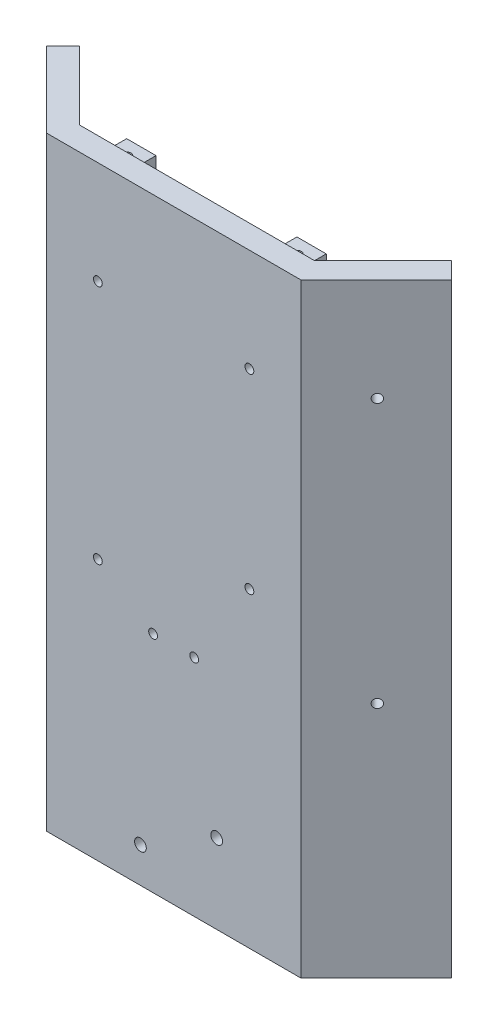
SolidWorks part; units mm, degrees
ref_plane "Front" through (0, 0, 0) normal (0, 0, 1) x (1, 0, 0)
ref_plane "Top" through (0, 0, 0) normal (0, 1, 0) x (1, 0, 0)
ref_plane "Right" through (0, 0, 0) normal (1, 0, 0) x (0, 0, -1)
sketch "Sketch1" plane through (0, 0, 0) normal (0, 1, 0) x (1, 0, 0)
  line L0 (-40, 0) -> (40, 0)
  line L1 (40, 0) -> (63.3345, 23.3345)
  line L2 (-40, 0) -> (-63.3345, 23.3345)
  line L3 (-43.3137, -8) -> (-68.9914, 17.6777)
  line L4 (-43.3137, -8) -> (43.3137, -8)
  line L5 (43.3137, -8) -> (68.9914, 17.6777)
  line L6 (-68.9914, 17.6777) -> (-63.3345, 23.3345)
  line L7 (68.9914, 17.6777) -> (63.3345, 23.3345)
  dimension "D1" = 80
  dimension "D2" = 33
  dimension "D3" = 33
  dimension "D4" = 135
  dimension "D5" = 135
  dimension "D6" = 8
extrude "Boss-Extrude1" add sketch "Sketch1" along normal blind 206
sketch "Sketch2" plane through (0, 0, 0) normal (0, 0, -1) x (-1, 0, 0)
  line L0 (-40, 206) -> (40, 206) construction
  line L1 (-34, 200) -> (-24, 200)
  line L2 (-34, 200) -> (-34, 194)
  line L3 (-34, 194) -> (-24, 194)
  line L4 (-24, 200) -> (-24, 194)
  line L5 (-34, 200) -> (-24, 194) construction
  line L6 (-34, 194) -> (-24, 200) construction
  line L7 (-40, 206) -> (-40, 0) construction
  line L8 (40, 206) -> (40, 0) construction
  line L9 (24, 200) -> (34, 200)
  line L10 (24, 200) -> (24, 194)
  line L11 (24, 194) -> (34, 194)
  line L12 (34, 200) -> (34, 194)
  line L13 (24, 200) -> (34, 194) construction
  line L14 (24, 194) -> (34, 200) construction
  point P0 (-29, 197)
  point P9 (29, 197)
  dimension "D1" = 6
  dimension "D2" = 10
  dimension "D3" = 6
  dimension "D4" = 6
  dimension "D5" = 6
  dimension "D6" = 10
  dimension "D7" = 6
  dimension "D8" = 6
extrude "Boss-Extrude2" add sketch "Sketch2" along normal blind 10
sketch "Sketch3" plane through (0, 200, 0) normal (0, 1, 0) x (1, 0, 0)
  line L0 (-34, 0) -> (-24, 10) construction
  line L1 (24, 0) -> (34, 10) construction
  circle A0 centre (-29, 5) radius 1.5
  circle A1 centre (29, 5) radius 1.5
  dimension "D1" = 3
  dimension "D2" = 3
extrude "Cut-Extrude1" cut sketch "Sketch3" against normal up to next
sketch "Sketch4" plane through (0, 0, 8) normal (0, 0, 1) x (1, 0, 0)
  line L0 (14.6671, 27) -> (-11.3137, 12) construction
  line L1 (-43.3137, 0) -> (43.3137, 0) construction
  line L3 (-43.3137, 206) -> (-43.3137, 0) construction
  circle A0 centre (-11.3137, 12) radius 2
  circle A1 centre (14.6671, 27) radius 2
  dimension "D2" = 4
  dimension "D3" = 4
  dimension "D1" = 30
  dimension "D4" = 12
  dimension "D5" = 30
  dimension "D6" = 32
extrude "Cut-Extrude2" cut sketch "Sketch4" against normal up to next
sketch "Sketch5" plane through (0, 0, 8) normal (0, 0, 1) x (1, 0, 0)
  line L0 (0, 0) -> (0, 76.4041) construction
  line L1 (-43.3137, 0) -> (43.3137, 0) construction
  line L2 (-11.3137, 12) -> (-67.2813, 108.9387) construction
  line L3 (0, 76.4041) -> (-36.3731, 55.4041) construction
  line L4 (-7, 76.4041) -> (7, 76.4041)
  circle A0 centre (0, 76.4041) radius 2 construction
  circle A1 centre (7, 76.4041) radius 1.5
  circle A2 centre (-7, 76.4041) radius 1.5
  dimension "D2" = 4
  dimension "D5" = 3
  dimension "D6" = 3
  dimension "D1" = 42
  dimension "D3" = 30
  dimension "D4" = 14
extrude "Cut-Extrude3" cut sketch "Sketch5" against normal up to next
sketch "Sketch6" plane through (0, 0, 8) normal (0, 0, 1) x (1, 0, 0)
  line L0 (-43.3137, 206) -> (43.3137, 206) construction
  line L1 (43.3137, 206) -> (43.3137, 0) construction
  line L2 (-43.3137, 206) -> (-43.3137, 0) construction
  circle A0 centre (25.8137, 171) radius 1.5
  circle A2 centre (-25.8137, 171) radius 1.5
  circle A3 centre (25.8137, 106) radius 1.5
  circle A4 centre (-25.8137, 89) radius 1.5
  dimension "D1" = 3
  dimension "D2" = 35
  dimension "D3" = 3
  dimension "D4" = 3
  dimension "D5" = 3
  dimension "D6" = 17.5
  dimension "D7" = 17.5
  dimension "D8" = 82
  dimension "D9" = 65
extrude "Cut-Extrude4" cut sketch "Sketch6" against normal up to next
sketch "Sketch7" plane through (25.6569, 0, 25.6569) normal (0.7071, 0, 0.7071) x (0.7071, 0, -0.7071)
  line L0 (24.9706, 206) -> (61.2843, 206) construction
  line L1 (24.9706, 206) -> (24.9706, 0) construction
  circle A0 centre (43.4106, 171) radius 1.5
  circle A1 centre (43.4106, 81) radius 1.5
  dimension "D1" = 3
  dimension "D2" = 3
  dimension "D5" = 90
  dimension "D3" = 35
  dimension "D4" = 18.44
extrude "Cut-Extrude5" cut sketch "Sketch7" against normal up to next and the other way through all
sketch "Sketch9" plane through (-25.6569, 0, 25.6569) normal (-0.7071, 0, 0.7071) x (0.7071, 0, 0.7071)
  line L0 (-61.2843, 206) -> (-24.9706, 206) construction
  line L1 (-61.2843, 206) -> (-61.2843, 0) construction
  circle A0 centre (-40.3843, 171) radius 1.5
  circle A1 centre (-40.3843, 76) radius 1.5
  dimension "D1" = 3
  dimension "D2" = 3
  dimension "D3" = 35
  dimension "D4" = 95
  dimension "D5" = 20.9
extrude "Cut-Extrude6" cut sketch "Sketch9" against normal up to next
